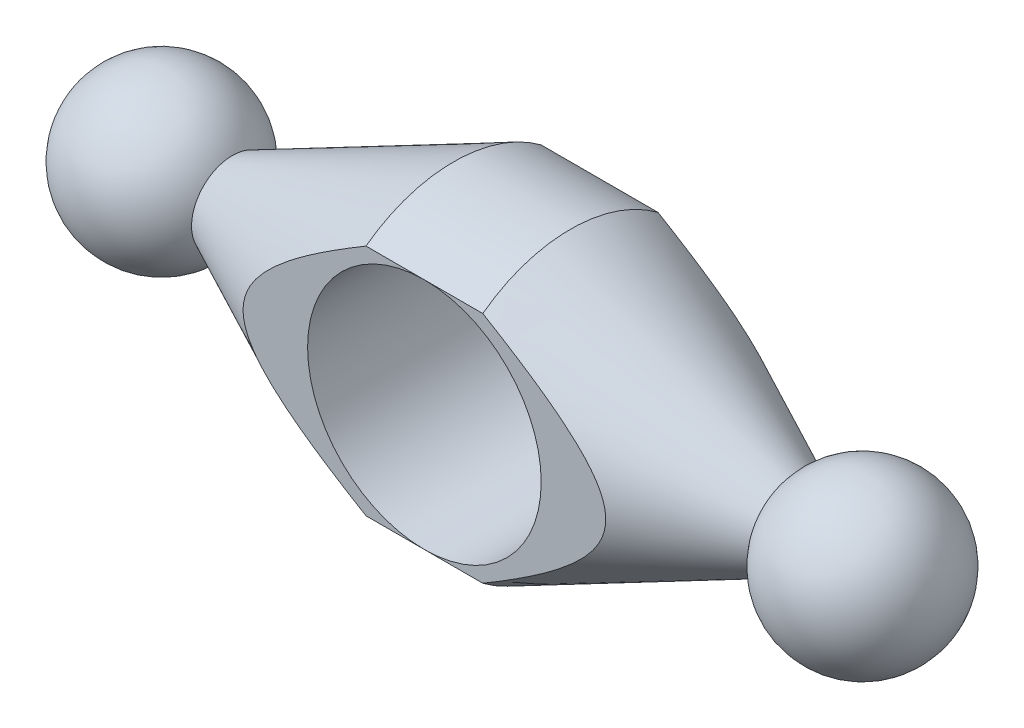
SolidWorks part; units mm, degrees
ref_plane "Спереди" through (0, 0, 0) normal (0, 0, 1) x (1, 0, 0)
ref_plane "Сверху" through (0, 0, 0) normal (0, 1, 0) x (1, 0, 0)
ref_plane "Справа" through (0, 0, 0) normal (1, 0, 0) x (0, 0, -1)
other "Configuration Table"
sketch "Эскиз1" plane through (0, 0, 0) normal (0, 0, 1) x (1, 0, 0)
  line L0 (0, 0) -> (301.8185, 0) construction
  line L1 (13.0622, 3.5) -> (32, 12.5)
  line L2 (32, 12.5) -> (42, 12.5)
  line L3 (37, 12.5) -> (37, 24.2241) construction
  line L4 (60.9378, 3.5) -> (42, 12.5)
  line L5 (0, 0) -> (74, 0)
  arc A0 (0, 0) -> (13.0622, 3.5) centre (7, 0) cw
  arc A1 (74, 0) -> (60.9378, 3.5) centre (67, 0) ccw
  dimension "D1" = 7
  dimension "D5" = 7
  dimension "D2" = 37
  dimension "D3" = 25
  dimension "D4" = 5
revolve "Повернуть1" add sketch "Эскиз1" angle 360 about L5
sketch "Эскиз2" plane through (0, 0, 0) normal (0, 0, 1) x (1, 0, 0)
  line L0 (0, 0) -> (79.6493, 0) construction
  line L1 (37, 0) -> (37, 26.1641) construction
  dimension "D1" = 37
ref_plane "Плоскость1" through (37, 0, 0) normal (1, 0, 0) x (0, 0, -1)
sketch "Эскиз4" plane through (37, 0, 0) normal (1, 0, 0) x (0, 0, -1)
  line L0 (-7.5, 10) -> (7.5, 10)
  line L1 (0, 0) -> (0, 26.1641) construction
  line L2 (7.5, 10) -> (7.5, 20)
  line L3 (7.5, 20) -> (15, 20)
  line L4 (15, 20) -> (15, 0)
  line L5 (0, 0) -> (29.9402, 0) construction
  line L6 (0, 0) -> (0, 17.1635) construction
  line L7 (-15, 20) -> (-15, 0)
  line L8 (-7.5, 20) -> (-15, 20)
  line L9 (-7.5, 10) -> (-7.5, 20)
  line L10 (15, 0) -> (-15, 0)
  point P15 (0, 10)
  dimension "D1" = 20
  dimension "D2" = 7.5
  dimension "D3" = 40
  dimension "D4" = 15
revolve "Вырез-Повернуть1" cut sketch "Эскиз4" angle 360 about L5
